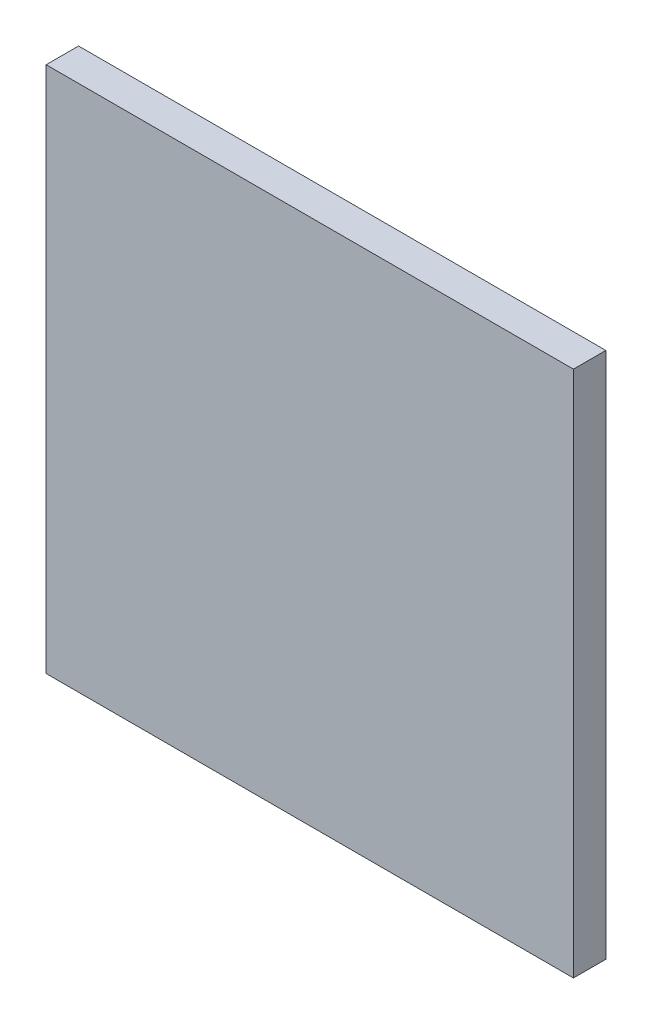
SolidWorks part; units mm, degrees
ref_plane "Front Plane" through (0, 0, 0) normal (0, 0, 1) x (1, 0, 0)
ref_plane "Top Plane" through (0, 0, 0) normal (0, 1, 0) x (1, 0, 0)
ref_plane "Right Plane" through (0, 0, 0) normal (1, 0, 0) x (0, 0, -1)
sketch "Sketch2" plane through (0, 0, 0) normal (0, 0, 1) x (1, 0, 0)
  line L0 (-58.9725, 0) -> (58.9725, 0) construction
  line L1 (0, 41.9985) -> (0, -41.9985) construction
  line L2 (-24.405, 24.405) -> (24.405, 24.405)
  line L3 (24.405, 24.405) -> (24.405, -24.405)
  line L4 (24.405, -24.405) -> (-24.405, -24.405)
  line L5 (-24.405, -24.405) -> (-24.405, 24.405)
  point P4 (0, 0)
  point P8 (0, 0)
  dimension "D1" = 48.81
extrude "Boss-Extrude1" add sketch "Sketch2" along normal blind 3
